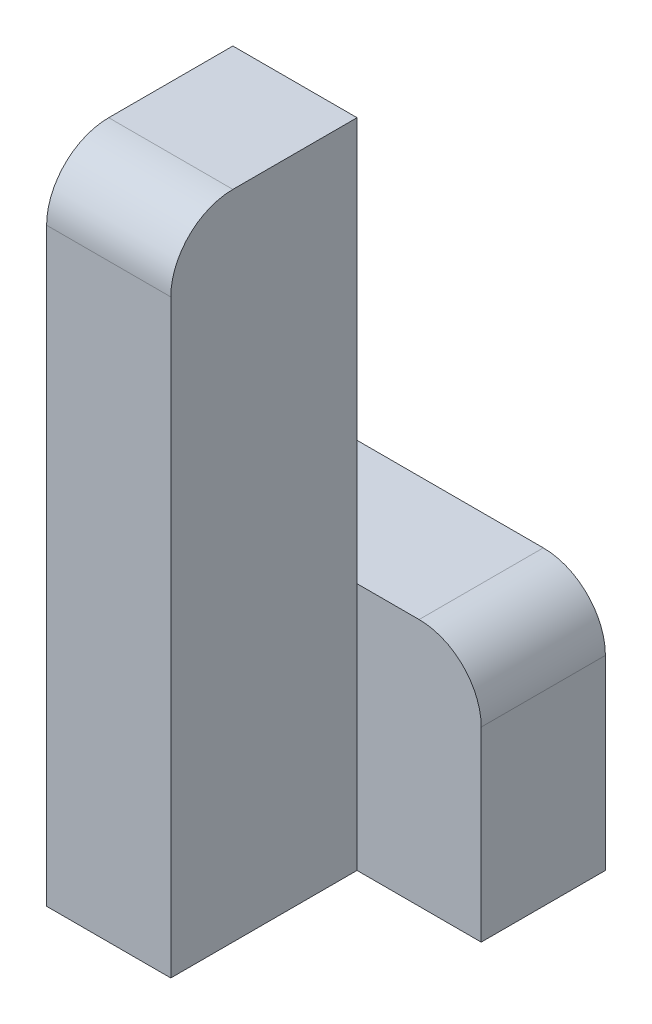
SolidWorks part; units mm, degrees
ref_plane "Front Plane" through (0, 0, 0) normal (0, 0, 1) x (1, 0, 0)
ref_plane "Top Plane" through (0, 0, 0) normal (0, 1, 0) x (1, 0, 0)
ref_plane "Right Plane" through (0, 0, 0) normal (1, 0, 0) x (0, 0, -1)
sketch "Sketch1" plane through (0, 0, 0) normal (0, 0, 1) x (1, 0, 0)
  line L1 (-30, -105) -> (-10, -105)
  line L2 (-10, -105) -> (-10, 0)
  line L3 (-10, 0) -> (-30, 0)
  line L4 (-30, 0) -> (-30, -105)
  dimension "D1" = 20
  dimension "Width" = 105
extrude "Boss-Extrude1" add sketch "Sketch1" along normal blind 30
sketch "Sketch2" plane through (0, 0, 0) normal (0, 0, 1) x (1, 0, 0)
  line L1 (-30, -105) -> (10, -105)
  line L2 (10, -105) -> (10, -65)
  line L3 (10, -65) -> (-30, -65)
  line L4 (-30, -65) -> (-30, -105)
  dimension "D1" = 40
  dimension "Width" = 40
extrude "Boss-Extrude2" add sketch "Sketch2" against normal blind 20
fillet "Fillet1" radius 10 2 edges at (10, -65, -10) (-20, 0, 30)
